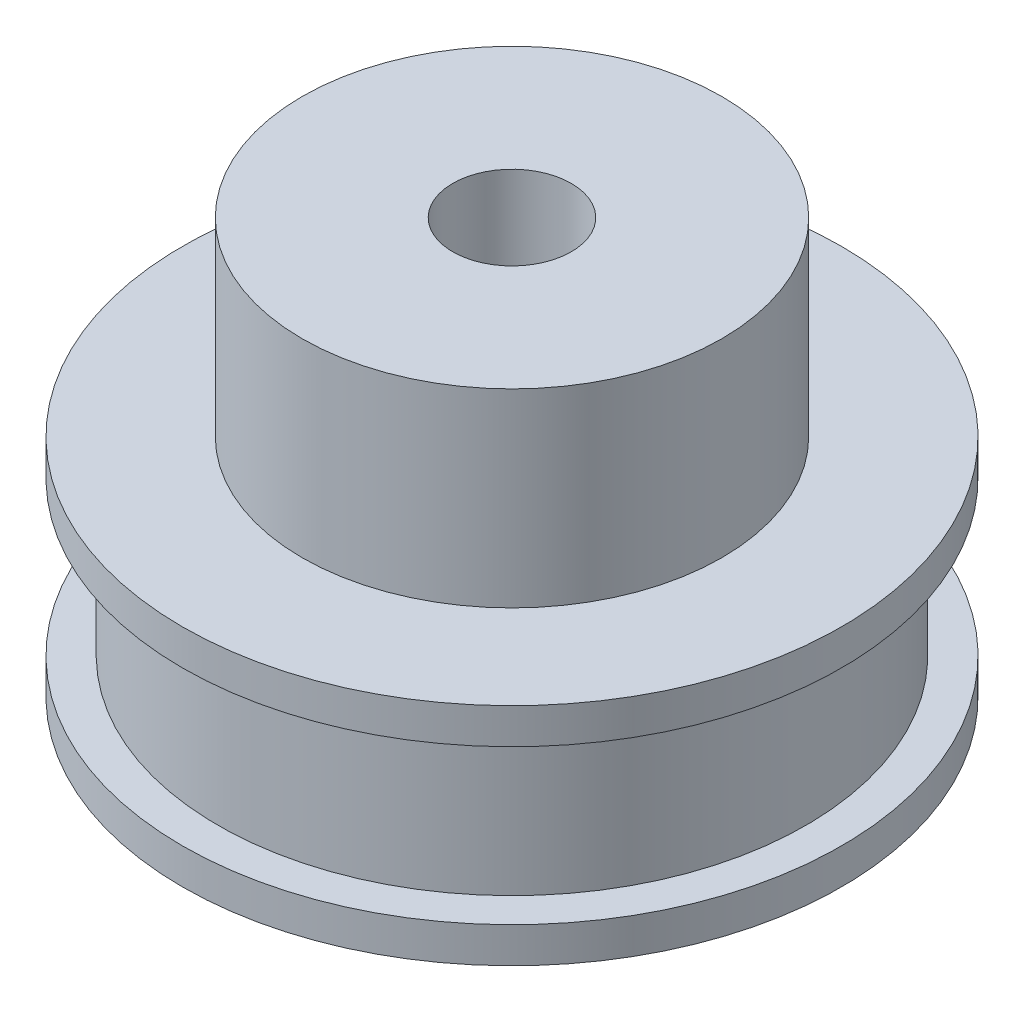
SolidWorks part; units mm, degrees
ref_plane "Face" through (0, 0, 0) normal (0, 0, 1) x (1, 0, 0)
ref_plane "Dessus" through (0, 0, 0) normal (0, 1, 0) x (1, 0, 0)
ref_plane "Droite" through (0, 0, 0) normal (1, 0, 0) x (0, 0, -1)
sketch "Esquisse1" plane through (0, 0, 0) normal (0, 0, 1) x (1, 0, 0)
  line L0 (0, 0) -> (0, 9.7978) construction
  line L1 (2.5, 0) -> (13.9, 0)
  line L2 (13.9, 0) -> (13.9, 1.5)
  line L3 (13.9, 1.5) -> (12.4, 1.5)
  line L4 (12.4, 1.5) -> (12.4, 8)
  line L5 (12.4, 8) -> (13.9, 8)
  line L6 (13.9, 8) -> (13.9, 9.5)
  line L7 (13.9, 9.5) -> (8.85, 9.5)
  line L8 (8.85, 9.5) -> (8.85, 17.5)
  line L9 (8.85, 17.5) -> (2.5, 17.5)
  line L10 (2.5, 17.5) -> (2.5, 0)
  dimension "D1" = 27.8
  dimension "D2" = 6.5
  dimension "D3" = 5
  dimension "D4" = 17.7
  dimension "D5" = 17.5
  dimension "D6" = 1.5
  dimension "D7" = 1.5
  dimension "D8" = 1.5
revolve "Révolution1" add sketch "Esquisse1" angle 360 about L0
